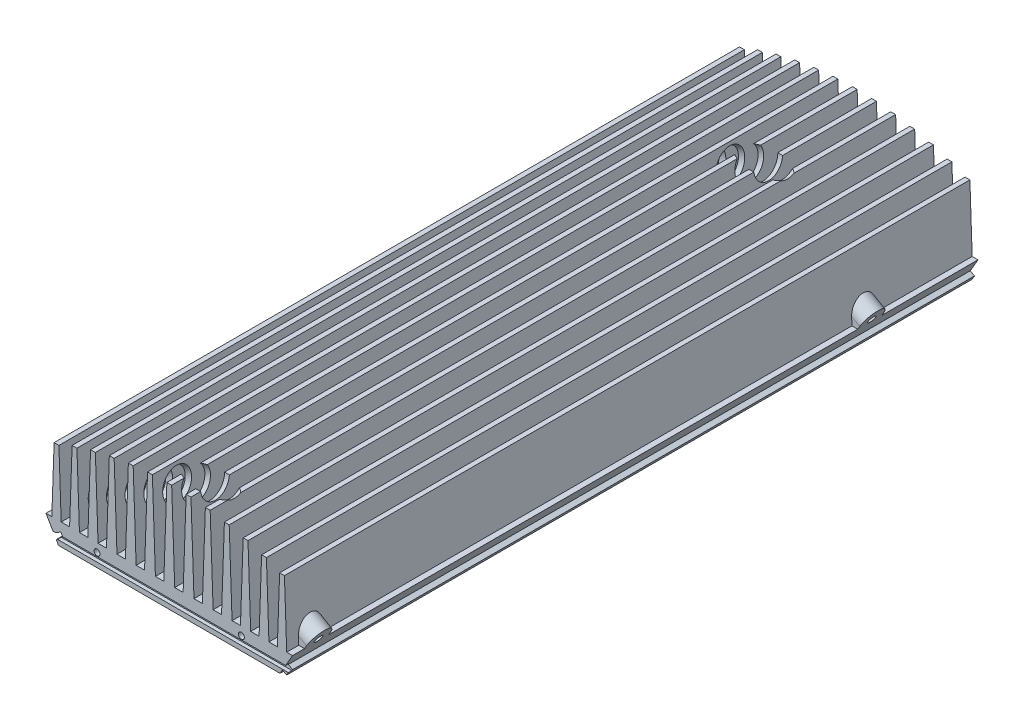
SolidWorks part; units mm, degrees
ref_plane "Plano frontal" through (0, 0, 0) normal (0, 0, 1) x (1, 0, 0)
ref_plane "Plano superior" through (0, 0, 0) normal (0, 1, 0) x (1, 0, 0)
ref_plane "Plano direito" through (0, 0, 0) normal (1, 0, 0) x (0, 0, -1)
sketch "Esboço1" plane through (0, 0, 0) normal (0, 0, 1) x (1, 0, 0)
  line L4 (0, 0) -> (-51.25, 88.7676) construction
  line L6 (-46.0538, 79.7676) -> (-51.25, 88.7676)
  line L20 (-48.8291, 88.7676) -> (-47.8825, 115.8751)
  line L21 (-47.8825, 115.8751) -> (-45.8825, 115.8751)
  line L22 (-45.8825, 115.8751) -> (-44.9359, 88.7676)
  line L23 (-44.9359, 88.7676) -> (-41.4359, 88.7676)
  line L24 (-41.4359, 88.7676) -> (-40.3931, 118.6305)
  line L25 (-40.3931, 118.6305) -> (-38.3931, 118.6305)
  line L26 (-38.3931, 118.6305) -> (-37.3502, 88.7676)
  line L27 (-37.3502, 88.7676) -> (-33.8502, 88.7676)
  line L28 (-33.8502, 88.7676) -> (-32.7279, 120.9063)
  line L29 (-32.7279, 120.9063) -> (-30.7279, 120.9063)
  line L30 (-30.7279, 120.9063) -> (-29.6056, 88.7676)
  line L31 (-29.6056, 88.7676) -> (-26.1056, 88.7676)
  line L32 (-26.1056, 88.7676) -> (-24.921, 122.6898)
  line L33 (-24.921, 122.6898) -> (-22.921, 122.6898)
  line L34 (-22.921, 122.6898) -> (-21.7364, 88.7676)
  line L37 (-21.7364, 88.7676) -> (-18.2364, 88.7676)
  line L38 (-18.2364, 88.7676) -> (-17.0071, 123.9709)
  line L39 (-17.0071, 123.9709) -> (-15.0071, 123.9709)
  line L40 (-15.0071, 123.9709) -> (-13.7778, 88.7676)
  line L42 (-13.7778, 88.7676) -> (-10.2778, 88.7676)
  line L43 (-10.2778, 88.7676) -> (-9.0215, 124.7424)
  line L44 (-9.0215, 124.7424) -> (-7.0215, 124.7424)
  line L45 (-7.0215, 124.7424) -> (-5.7653, 88.7676)
  line L46 (-5.7653, 88.7676) -> (-2.2653, 88.7676)
  line L47 (-2.2653, 88.7676) -> (-1, 125)
  line L50 (0, 0) -> (0, 125) construction
  line L90 (0, 0) -> (-140.069, 0) construction
  line L91 (-46.0538, 79.7676) -> (46.0538, 79.7676)
  line L127 (46.0538, 79.7676) -> (51.25, 88.7676)
  line L128 (2.2653, 88.7676) -> (1, 125)
  line L129 (5.7653, 88.7676) -> (2.2653, 88.7676)
  line L130 (7.0215, 124.7424) -> (5.7653, 88.7676)
  line L131 (9.0215, 124.7424) -> (7.0215, 124.7424)
  line L132 (10.2778, 88.7676) -> (9.0215, 124.7424)
  line L133 (13.7778, 88.7676) -> (10.2778, 88.7676)
  line L134 (15.0071, 123.9709) -> (13.7778, 88.7676)
  line L135 (17.0071, 123.9709) -> (15.0071, 123.9709)
  line L136 (18.2364, 88.7676) -> (17.0071, 123.9709)
  line L137 (21.7364, 88.7676) -> (18.2364, 88.7676)
  line L138 (22.921, 122.6898) -> (21.7364, 88.7676)
  line L139 (24.921, 122.6898) -> (22.921, 122.6898)
  line L140 (26.1056, 88.7676) -> (24.921, 122.6898)
  line L141 (29.6056, 88.7676) -> (26.1056, 88.7676)
  line L142 (30.7279, 120.9063) -> (29.6056, 88.7676)
  line L143 (32.7279, 120.9063) -> (30.7279, 120.9063)
  line L144 (33.8502, 88.7676) -> (32.7279, 120.9063)
  line L145 (37.3502, 88.7676) -> (33.8502, 88.7676)
  line L146 (38.3931, 118.6305) -> (37.3502, 88.7676)
  line L147 (40.3931, 118.6305) -> (38.3931, 118.6305)
  line L148 (41.4359, 88.7676) -> (40.3931, 118.6305)
  line L149 (44.9359, 88.7676) -> (41.4359, 88.7676)
  line L150 (45.8825, 115.8751) -> (44.9359, 88.7676)
  line L151 (47.8825, 115.8751) -> (45.8825, 115.8751)
  line L152 (48.8291, 88.7676) -> (47.8825, 115.8751)
  line L153 (51.25, 88.7676) -> (48.8291, 88.7676)
  line L154 (-1, 125) -> (1, 125)
  line L155 (-51.25, 88.7676) -> (-48.8291, 88.7676)
  circle A0 centre (0, 0) radius 125 construction
  point P5 (0, 125)
  point P9 (-46.8825, 115.8751)
  point P19 (0, 79.7676)
  point P68 (-39.3931, 118.6305)
  point P69 (-31.7279, 120.9063)
  point P70 (-23.921, 122.6898)
  point P71 (-16.0071, 123.9709)
  point P80 (-8.0215, 124.7424)
  dimension "D1" = 250
  dimension "D2" = 9
  dimension "D3" = 60
  dimension "D4" = 3.5
  dimension "D5" = 2
  dimension "D6" = 92
  dimension "D7" = 92
  dimension "D9" = 51.25
extrude "Ressalto-extrusão1" add sketch "Esboço1" along normal blind 285
sketch "Esboço2" plane through (0, 0, 285) normal (0, 0, 1) x (1, 0, 0)
  line L0 (-47.0038, 81.4131) -> (-43.9728, 83.1631)
  line L1 (-48.1038, 83.3183) -> (-48.0538, 83.2317) construction
  line L2 (-43.9728, 83.1631) -> (-45.0728, 85.0683)
  line L3 (-47.0538, 81.4997) -> (-47.0038, 81.4131) construction
  line L5 (-48.1038, 83.3183) -> (-45.0728, 85.0683)
  line L6 (-48.1038, 83.3183) -> (-47.0038, 81.4131)
  line L7 (-51.25, 88.7676) -> (-46.0538, 79.7676) construction
  dimension "D1" = 2
  dimension "D2" = 3.5
  dimension "D3" = 2
  dimension "D4" = 0.1
extrude "Corte-extrusão1" cut sketch "Esboço2" against normal through all
sketch "Esboço3" plane through (0, 0, 285) normal (0, 0, 1) x (1, 0, 0)
  line L1 (46.0538, 79.7676) -> (51.25, 88.7676) construction
  line L6 (47.0538, 81.4997) -> (48.0538, 83.2317)
  line L10 (48.0538, 83.2317) -> (49.7859, 82.2317)
  line L11 (49.7859, 82.2317) -> (48.7859, 80.4997)
  line L12 (48.7859, 80.4997) -> (47.0538, 81.4997)
  dimension "D1" = 2
  dimension "D2" = 2
  dimension "D3" = 2
extrude "Ressalto-extrusão3" add sketch "Esboço3" against normal blind 285 separate body
sketch "Esboço13" plane through (0, 0, 0) normal (1, 0, 0) x (0, 0, -1)
  line L0 (-285, 83.7676) -> (-283.5, 83.7676)
  line L1 (-283.5, 83.7676) -> (-283.5, 81.7676)
  line L2 (-283.5, 81.7676) -> (-285, 81.7676)
  line L3 (-285, 81.7676) -> (-285, 83.7676)
  line L4 (-285, 79.7676) -> (0, 79.7676) construction
  line L5 (-285, 85.0683) -> (-285, 83.3183) construction
  dimension "D1" = 2
  dimension "D2" = 2
  dimension "D3" = 1.5
extrude "Corte-extrusão7" cut sketch "Esboço13" against normal through all both and the other way through all
sketch "Esboço8" plane through (0, 0, 0) normal (0.866, -0.5, 0) x (0, 0, -1)
  line L0 (-280, 104.1077) -> (-280, 96.1077)
  line L1 (-280, 96.1077) -> (-270, 96.1077)
  line L2 (-270, 96.1077) -> (-270, 104.1077)
  line L4 (0, 96.1077) -> (-283.5, 96.1077) construction
  line L5 (0, 96.1077) -> (-283.5, 96.1077) construction
  line L6 (-285, 96.7265) -> (-285, 102.5) construction
  arc A0 (-280, 104.1077) -> (-270, 104.1077) centre (-275, 104.1077) cw
  dimension "D1" = 5
  dimension "D4" = 8
  dimension "D2" = 10
  dimension "D3" = 5
  dimension "D5" = 8
  dimension "D6" = 8
extrude "Ressalto-extrusão5" add sketch "Esboço8" against normal blind 10
sketch "Esboço5" plane through (0, 0, 285) normal (0, 0, 1) x (1, 0, 0)
  line L0 (-46.0538, 79.7676) -> (46.0538, 79.7676) construction
  circle A0 centre (-30, 85.2676) radius 1.25
  circle A1 centre (30, 85.2676) radius 1.25
  dimension "D1" = 2.5
  dimension "D2" = 21.25
  dimension "D3" = 5.5
  dimension "D4" = 2.5
  dimension "D5" = 21.25
  dimension "D6" = 5.5
extrude "Corte-extrusão3" cut sketch "Esboço5" against normal blind 10
sketch "Esboço6" plane through (0, 0, 0) normal (-0.866, -0.5, 0) x (0, 0, 1)
  line L0 (280, 104.2077) -> (280, 96.3093)
  line L1 (280, 96.3093) -> (270, 96.3093)
  line L2 (270, 96.3093) -> (270, 104.2077)
  line L5 (285, 102.5) -> (285, 96.7265) construction
  line L6 (0, 96.2077) -> (283.5, 96.2077) construction
  arc A0 (270, 104.2077) -> (280, 104.2077) centre (275, 104.2077) cw
  dimension "D2" = 5
  dimension "D1" = 5
  dimension "D3" = 10
  dimension "D5" = 8
extrude "Ressalto-extrusão4" add sketch "Esboço6" against normal blind 11
sketch "Esboço7" plane through (0, 0, 0) normal (-0.866, -0.5, 0) x (0, 0, 1)
  circle A0 centre (275, 104.2077) radius 2.25
  dimension "D1" = 4.5
extrude "Corte-extrusão4" cut sketch "Esboço7" against normal blind 12
sketch "Esboço9" plane through (0, 0, 0) normal (0.866, -0.5, 0) x (0, 0, -1)
  circle A0 centre (-275, 104.1077) radius 1.65
  dimension "D1" = 3.3
extrude "Corte-extrusão5" cut sketch "Esboço9" against normal blind 10
sketch "Esboço10" plane through (0, 0, 0) normal (0, 0, -1) x (-1, 0, 0)
  line L0 (9.3622, 114.9876) -> (9.3622, 88.7676)
  line L2 (9.3622, 88.7676) -> (-9.3622, 88.7676)
  line L3 (-9.3622, 88.7676) -> (-9.3622, 114.9876)
  line L4 (9.0215, 124.7424) -> (10.2778, 88.7676) construction
  line L6 (-10.2778, 88.7676) -> (-9.0215, 124.7424) construction
  line L8 (2.2653, 88.7676) -> (5.7653, 88.7676) construction
  line L10 (-9.3622, 114.9876) -> (9.3622, 114.9876)
  dimension "D1" = 26.22
extrude "Ressalto-extrusão6" add sketch "Esboço10" against normal blind 15
sketch "Esboço12" plane through (0, 0, 0) normal (0, 0, -1) x (-1, 0, 0)
  line L0 (46.0538, 79.7676) -> (-46.0538, 79.7676) construction
  line L1 (0, 125) -> (0, 79.7676) construction
  line L2 (-1, 125) -> (1, 125) construction
  circle A0 centre (0, 105) radius 2.5
  dimension "D1" = 5
  dimension "D2" = 25.2324
extrude "Corte-extrusão8" cut sketch "Esboço12" against normal blind 20
sketch "Esboço14" plane through (0, 0, 0) normal (-0.866, -0.5, 0) x (0, 0, 1)
  circle A0 centre (275, 104.2077) radius 6
  dimension "D1" = 12
extrude "Corte-extrusão9" cut sketch "Esboço14" against normal blind 100 from offset 11 offset against normal yes
pattern_linear "Padrão linear1" count 2 spacing 230 along (0, 0, -1) of "Corte-extrusão4", "Ressalto-extrusão4", "Corte-extrusão9", "Ressalto-extrusão5", "Corte-extrusão5"
sketch "Esboço15" plane through (0, 79.7676, 0) normal (0, -1, 0) x (1, 0, 0)
  circle A0 centre (36.5, 246.65) radius 1.65
  circle A1 centre (-36.5, 246.65) radius 1.65
  circle A2 centre (38.145, 142.066) radius 1.65
  circle A3 centre (32.5, 12.65) radius 1.65
  circle A4 centre (-38.5, 26.15) radius 1.65
  circle A5 centre (-15.83, 8.335) radius 1.25
  circle A6 centre (-15.449, 26.242) radius 1.25
  circle A7 centre (25.572, 49.15) radius 1.25
  circle A8 centre (21.762, 76.661) radius 1.25
  circle A9 centre (-25.863, 97.743) radius 1.25
  circle A10 centre (-22.307, 180.42) radius 1.25
  circle A11 centre (27.096, 173.943) radius 1.25
  circle A12 centre (21.254, 234.65) radius 1.25
  circle A13 centre (17.5, 217.65) radius 1.25
  circle A14 centre (17.5, 197.65) radius 1.25
  circle A15 centre (17.5, 177.65) radius 1.25
  circle A16 centre (17.5, 157.65) radius 1.25
  circle A17 centre (-17.5, 127.65) radius 1.25
  circle A18 centre (-17.5, 107.65) radius 1.25
  circle A19 centre (-17.5, 87.65) radius 1.25
  circle A20 centre (-17.5, 67.65) radius 1.25
  dimension "D1" = 3.3
  dimension "D2" = 2.5
extrude "Corte-extrusão10" cut sketch "Esboço15" against normal blind 8
